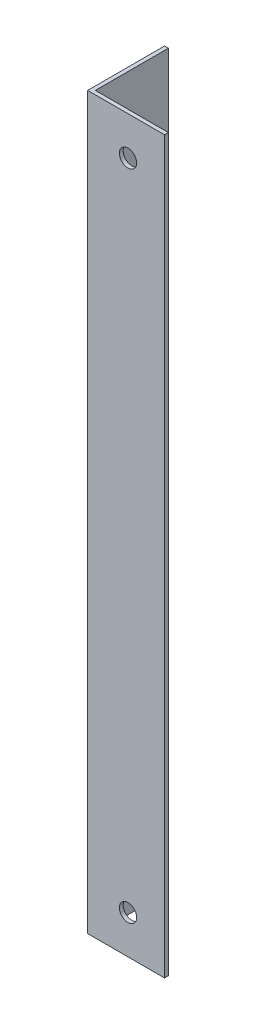
SolidWorks part; units mm, degrees
material "1060 Сплав"
ref_plane "Спереди" through (0, 0, 0) normal (0, 0, 1) x (1, 0, 0)
ref_plane "Сверху" through (0, 0, 0) normal (0, 1, 0) x (1, 0, 0)
ref_plane "Справа" through (0, 0, 0) normal (1, 0, 0) x (0, 0, -1)
sketch "Эскиз1" plane through (0, 0, 0) normal (0, 1, 0) x (1, 0, 0)
  line L0 (0, 0) -> (0, 20)
  line L1 (0, 20) -> (1, 20)
  line L2 (1, 20) -> (1, 1)
  line L3 (1, 1) -> (20, 1)
  line L4 (20, 1) -> (20, 0)
  line L5 (20, 0) -> (0, 0)
  dimension "D1" = 1
  dimension "D2" = 20
extrude "Бобышка-Вытянуть1" add sketch "Эскиз1" along normal blind 190
sketch "Эскиз2" plane through (0, 0, -1) normal (0, 0, -1) x (-1, 0, 0)
  line L0 (-10.5, 190) -> (-10.5, 0) construction
  line L1 (-20, 190) -> (-1, 190) construction
  line L2 (-20, 0) -> (-1, 0) construction
  circle A0 centre (-10.5, 10) radius 2.25
  circle A1 centre (-10.5, 180) radius 2.25
  dimension "D1" = 4.5
  dimension "D3" = 4.5
  dimension "D4" = 10
  dimension "D2" = 10
extrude "Вырез-Вытянуть1" cut sketch "Эскиз2" against normal through all
sketch "Sketch1" plane through (1, 0, 0) normal (1, 0, 0) x (0, 0, -1)
  line L0 (20, 190) -> (20, 0) construction
  line L1 (1, 190) -> (20, 190) construction
  line L2 (7, 155) -> (7, 114.2188) construction
  circle A0 centre (7, 155) radius 1.6
  circle A1 centre (7, 122) radius 1.6
  dimension "D1" = 33
  dimension "D2" = 3.2
  dimension "D3" = 3.2
  dimension "D4" = 13
  dimension "D6" = 35
extrude "Cut-Extrude1" cut sketch "Sketch1" against normal through all
